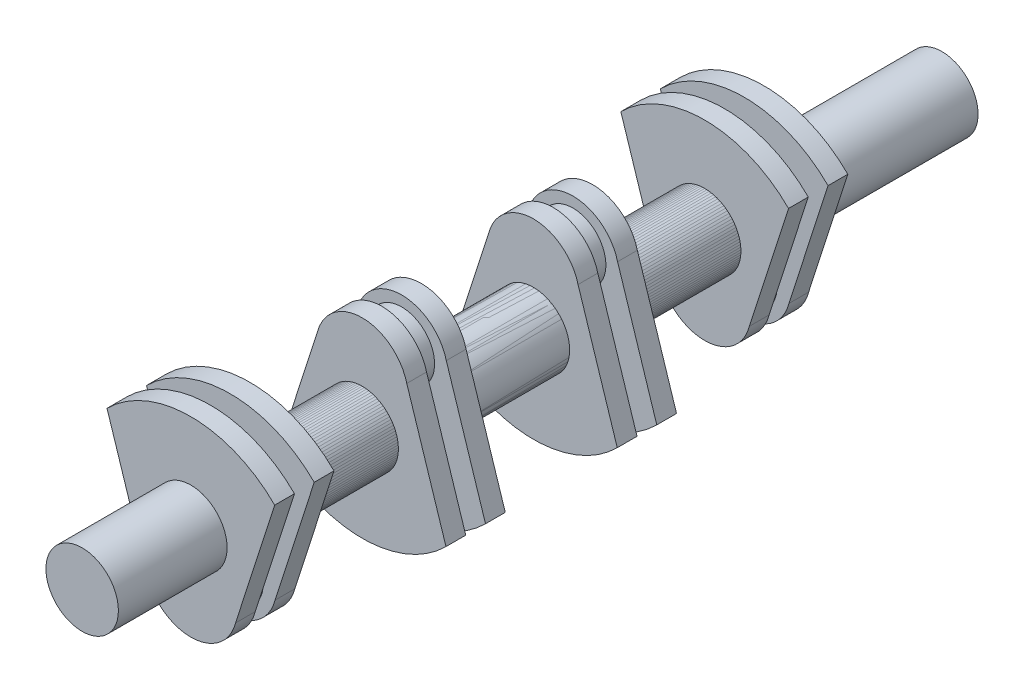
SolidWorks part; units mm, degrees
ref_plane "Front Plane" through (0, 0, 0) normal (0, 0, 1) x (1, 0, 0)
ref_plane "Top Plane" through (0, 0, 0) normal (0, 1, 0) x (1, 0, 0)
ref_plane "Right Plane" through (0, 0, 0) normal (1, 0, 0) x (0, 0, -1)
sketch "Sketch1" plane through (0, 0, 0) normal (0, 0, 1) x (1, 0, 0)
  line L0 (0, -37.2371) -> (0, 38.6317) construction
  line L1 (-42.1184, 0) -> (49.3705, 0) construction
  line L3 (-63.6396, 58.6396) -> (-33.889, -33.7485)
  line L4 (63.6396, 58.6396) -> (33.889, -33.7485)
  arc A0 (-33.889, -33.7485) -> (33.889, -33.7485) centre (0, -25) ccw
  arc A1 (-63.6396, 58.6396) -> (63.6396, 58.6396) centre (0, -5) cw
  dimension "D2" = 70
  dimension "D3" = 90
  dimension "D4" = 20
extrude "Boss-Extrude1" add sketch "Sketch1" along normal blind 15
sketch "Sketch3" plane through (0, 0, 15) normal (0, 0, 1) x (1, 0, 0)
  line L0 (0, 0) -> (0, -27.1041) construction
  circle A2 centre (0, -27.1041) radius 25
  dimension "D1" = 50
extrude "Boss-Extrude2" add sketch "Sketch3" against normal blind 30
sketch "Sketch4" plane through (0, 0, 15) normal (0, 0, 1) x (1, 0, 0)
  line L0 (0, 85) -> (0, -60) construction
  arc A0 (63.6396, 58.6396) -> (-63.6396, 58.6396) centre (0, -5) ccw construction
  arc A1 (-33.889, -33.7485) -> (33.889, -33.7485) centre (0, -25) ccw construction
  circle A2 centre (0, 12.5) radius 27.5
  dimension "D1" = 55
extrude "Boss-Extrude3" add sketch "Sketch4" along normal blind 85
ref_plane "Plane6" through (0, 0, -7.5) normal (0, 0, -1) x (-1, 0, 0)
mirror "Mirror5" about plane through (0, 0, -7.5) normal (0, 0, -1) of bodies 103
ref_plane "Plane7" through (0, 0, -72.5) normal (0, 0, -1) x (-1, 0, 0)
mirror "Mirror6" about plane through (0, 0, -72.5) normal (0, 0, -1) of bodies 111
move or copy body "Body-Move/Copy3" bodies to move or copy 112 copy no rotation origin (0, 12.5, 0) rotation axis (0, 0, 1) rotation angle 180
ref_plane "Plane8" through (0, 0, -202.5) normal (0, 0, -1) x (-1, 0, 0)
mirror "Mirror7" about plane through (0, 0, -202.5) normal (0, 0, -1) of bodies 113
mirror "Mirror9" about plane through (0, 0, -202.5) normal (0, 0, -1) of bodies 111
sketch "Sketch5" plane through (0, 0, 100) normal (0, 0, 1) x (1, 0, 0)
  circle A0 centre (0, 12.5) radius 27.5
  dimension "D1" = 55
sketch "Sketch6" plane through (0, 0, -202.5) normal (0, 0, -1) x (-1, 0, 0)
  circle A0 centre (0, 12.5) radius 27.5
extrude "Boss-Extrude5" add sketch "Sketch6" along normal blind 50 from surface at 302.5 starting at face at (27.5, 12.5, -505)
extrude "Cut-Extrude4" cut sketch "Sketch5" against normal blind 2.5
